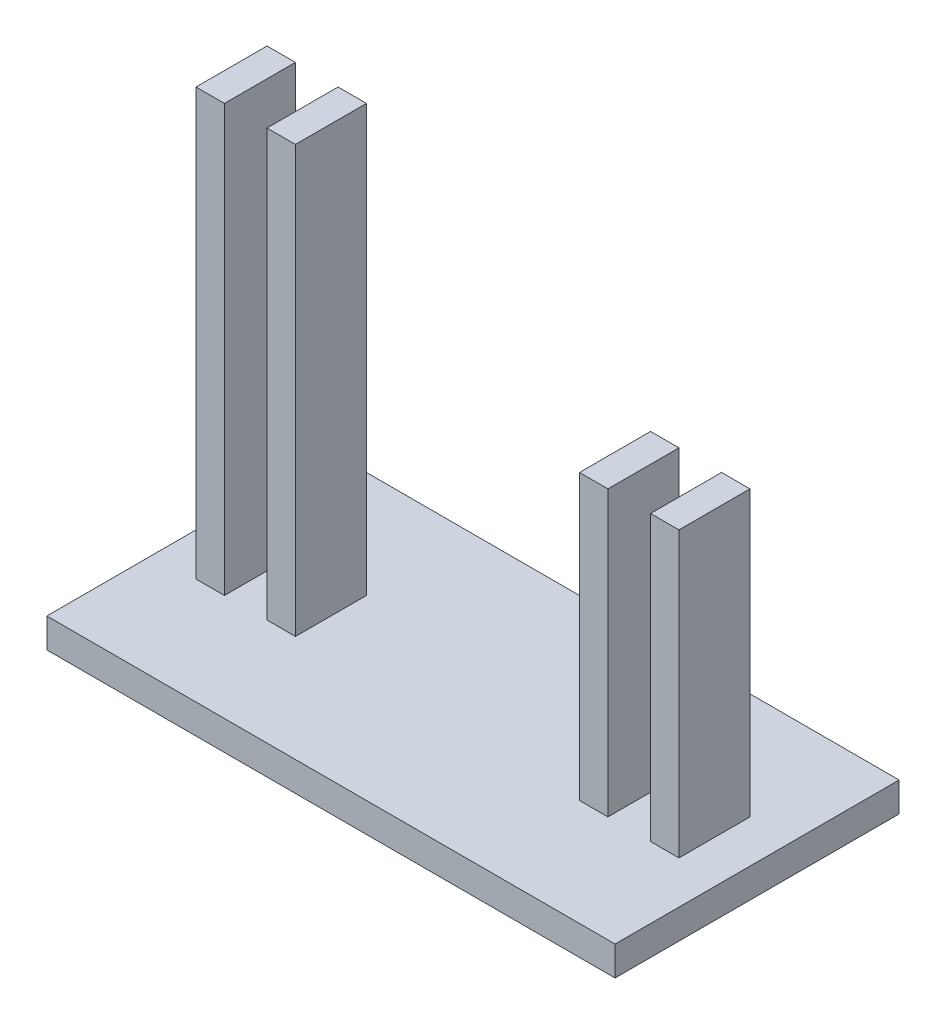
SolidWorks part; units mm, degrees
ref_plane "Front Plane" through (0, 0, 0) normal (0, 0, 1) x (1, 0, 0)
ref_plane "Top Plane" through (0, 0, 0) normal (0, 1, 0) x (1, 0, 0)
ref_plane "Right Plane" through (0, 0, 0) normal (1, 0, 0) x (0, 0, -1)
sketch "Sketch2" plane through (0, 0, 0) normal (0, 1, 0) x (1, 0, 0)
  line L0 (-100, 50) -> (100, 50)
  line L2 (-100, 50) -> (-100, -50)
  line L3 (-100, -50) -> (100, -50)
  line L4 (100, -50) -> (100, 50)
  dimension "D1" = 200
  dimension "D2" = 100
extrude "Boss-Extrude1" add sketch "Sketch2" along normal blind 10.3577
sketch "Sketch4" plane through (0, 10.3577, 0) normal (0, 1, 0) x (1, 0, 0)
  line L0 (-75, 12.5) -> (-75, -12.5)
  line L1 (0, 0) -> (-132.337, 0) construction
  line L3 (0, 62.6926) -> (0, -69.3143) construction
  line L4 (-75, 12.5) -> (-85, 12.5)
  line L5 (-85, 12.5) -> (-85, -12.5)
  line L6 (-85, -12.5) -> (-75, -12.5)
  line L7 (-60, 12.5) -> (-60, -12.5)
  line L8 (-60, -12.5) -> (-50, -12.5)
  line L9 (-50, -12.5) -> (-50, 12.5)
  line L10 (-50, 12.5) -> (-60, 12.5)
  dimension "D1" = 10
  dimension "D2" = 10
  dimension "D3" = 25
  dimension "D4" = 25
  dimension "D5" = 50
  dimension "D6" = 15
sketch "Sketch5" plane through (0, 10.3577, 0) normal (0, 1, 0) x (1, 0, 0)
extrude "Boss-Extrude2" add sketch "Sketch4" along normal blind 150
sketch "Sketch7" plane through (0, 10.3577, 0) normal (0, 1, 0) x (1, 0, 0)
  line L8 (0, 61.9098) -> (0, -69.1807) construction
  line L13 (75, 12.5) -> (75, -12.5)
  line L14 (85, -12.5) -> (75, -12.5)
  line L15 (85, 12.5) -> (85, -12.5)
  line L16 (85, 12.5) -> (75, 12.5)
  line L17 (60, -12.5) -> (60, 12.5)
  line L18 (50, -12.5) -> (60, -12.5)
  line L19 (50, 12.5) -> (50, -12.5)
  line L20 (60, 12.5) -> (50, 12.5)
extrude "Boss-Extrude3" add sketch "Sketch7" along normal blind 100
